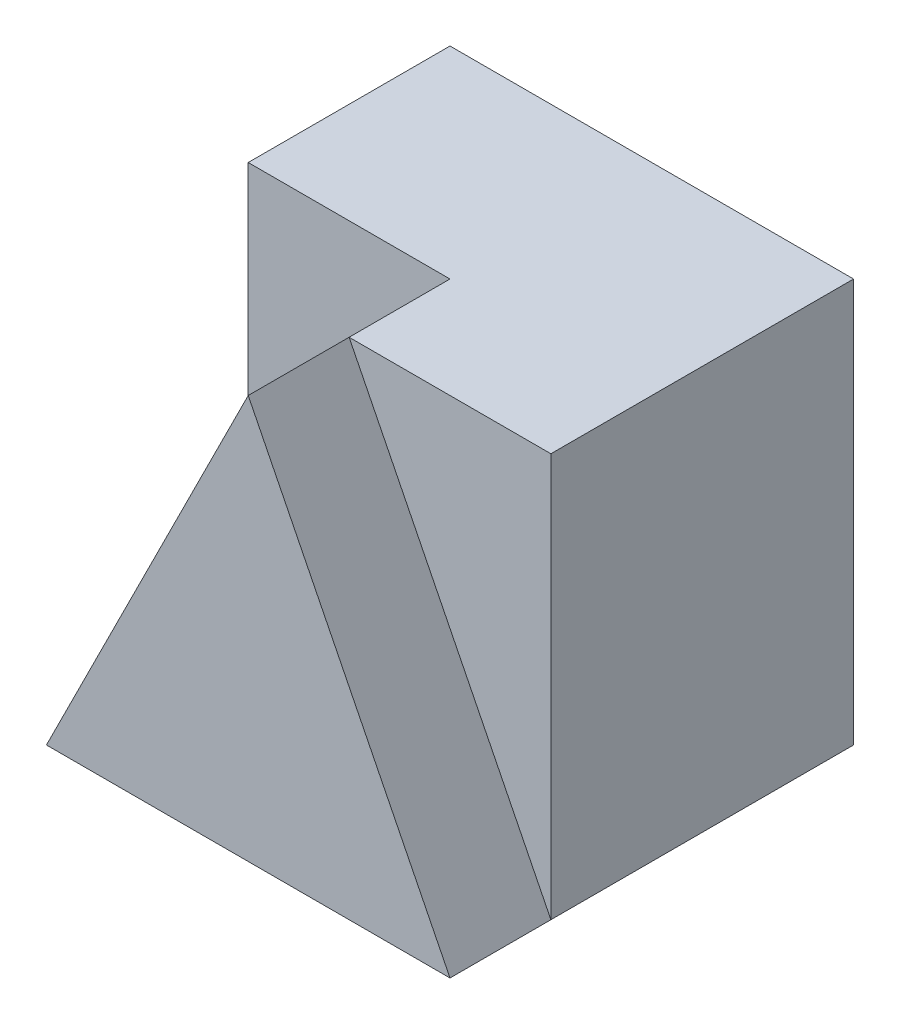
SolidWorks part; units mm, degrees
ref_plane "Front" through (0, 0, 0) normal (0, 0, 1) x (1, 0, 0)
ref_plane "Top" through (0, 0, 0) normal (0, 1, 0) x (1, 0, 0)
ref_plane "Right" through (0, 0, 0) normal (1, 0, 0) x (0, 0, -1)
sketch "Sketch1" plane through (0, 0, 0) normal (0, 1, 0) x (1, 0, 0)
  line L1 (-2, -2) -> (2, -2)
  line L2 (-2, -2) -> (-2, 2)
  line L3 (-2, 2) -> (2, 2)
  line L4 (2, -2) -> (2, 2)
  line L5 (-2, -2) -> (2, 2) construction
  line L6 (-2, 2) -> (2, -2) construction
  point P0 (0, 0)
  dimension "D1" = 4
  dimension "D2" = 4
extrude "Boss-Extrude1" add sketch "Sketch1" along normal blind 4
sketch "Sketch4" plane through (0, 0, 2) normal (0, 0, 1) x (1, 0, 0)
  line L0 (0, 4) -> (2, 4)
  line L1 (-2, 4) -> (2, 4) construction
  line L2 (2, 4) -> (2, 0)
  line L3 (2, 0) -> (0, 4)
extrude "Cut-Extrude1" cut sketch "Sketch4" against normal blind 1
sketch "Sketch5" plane through (0, 0, 2) normal (0, 0, 1) x (1, 0, 0)
  line L0 (0, 4) -> (-2, 0)
  line L1 (-2, 0) -> (-2, 4)
  line L2 (-2, 4) -> (0, 4)
extrude "Cut-Extrude2" cut sketch "Sketch5" against normal blind 2
